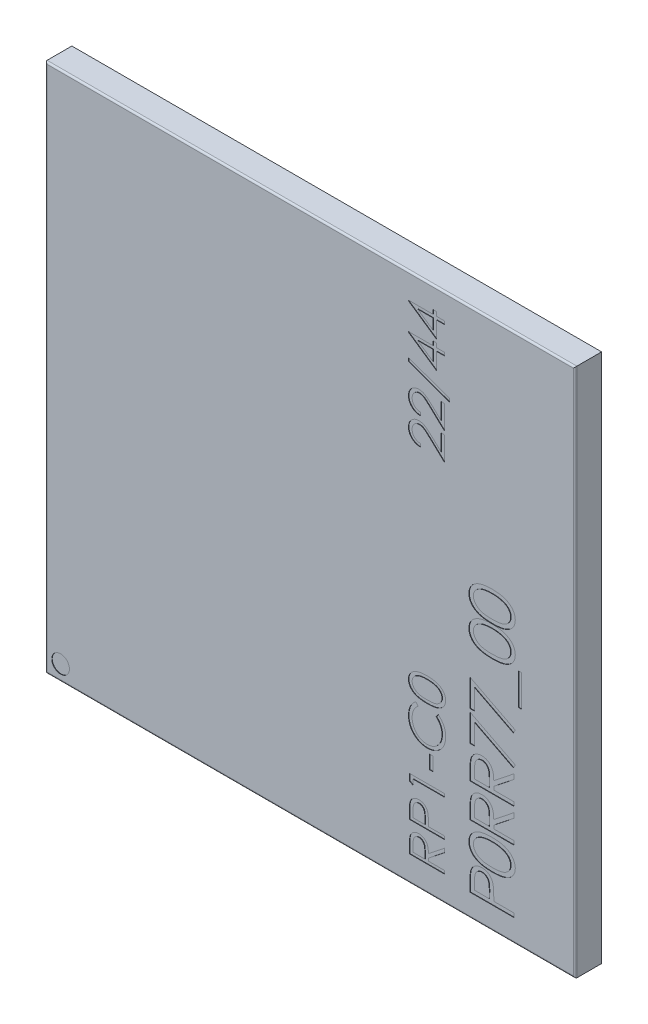
SolidWorks part; units mm, degrees
ref_plane "Płaszczyzna przednia" through (0, 0, 0) normal (0, 0, 1) x (1, 0, 0)
ref_plane "Płaszczyzna górna" through (0, 0, 0) normal (0, 1, 0) x (1, 0, 0)
ref_plane "Płaszczyzna prawa" through (0, 0, 0) normal (1, 0, 0) x (0, 0, -1)
sketch "Sketch1" plane through (0, 0, 0) normal (0, 0, 1) x (1, 0, 0)
  line L1 (6, -6) -> (-6, -6)
  line L2 (6, -6) -> (6, 6)
  line L3 (6, 6) -> (-6, 6)
  line L4 (-6, -6) -> (-6, 6)
  line L5 (6, -6) -> (-6, 6) construction
  line L6 (6, 6) -> (-6, -6) construction
  point P0 (0, 0)
  dimension "D1" = 12
extrude "Boss-Extrude1" add sketch "Sketch1" along normal blind 0.6
fillet "Fillet1" radius 0.04 4 edges at (0, 6, 0.6) (6, 0, 0.6) (0, -6, 0.6) (-6, 0, 0.6)
sketch "Sketch2" plane through (0, 0, 0.6) normal (0, 0, 1) x (1, 0, 0)
  line L0 (1.5285, -1.7789) -> (1.5285, 2.8946) construction
  text T0 "rr"
sketch "Sketch3" plane through (0, 0, 0) normal (0, 0, -1) x (-1, 0, 0)
  line L0 (5.3, -6) -> (5.3, -6.45)
  line L1 (-6, -6) -> (6, -6) construction
  line L2 (5.3, -6.45) -> (5.1, -6.45)
  line L3 (5.1, -6.45) -> (5.1, -6)
  line L4 (5.1, -6) -> (5.3, -6)
  line L5 (6, -6) -> (6, 6) construction
  dimension "D1" = 0.7
  dimension "D2" = 0.2
  dimension "D3" = 0.45
sketch "Sketch5" plane through (0, 0, 0) normal (0, 0, -1) x (-1, 0, 0)
  circle A0 centre (0, 0) radius 2.5
  dimension "D1" = 5
extrude "Boss-Extrude3" add sketch "Sketch5" along normal blind 0.1 separate body
sketch "Szkic1" plane through (0, 0, 0.6) normal (0, 0, 1) x (1, 0, 0)
  line L0 (-49.5686, 13.902) -> (-49.5686, 85.2353) construction
  line L1 (-2.0166, -2.1471) -> (-2.0166, -1.5732)
  line L2 (-2.0166, -1.5732) -> (-1.3854, -1.5732)
  line L3 (-1.3854, -1.5732) -> (-2.0121, -0.9673)
  line L4 (-2.0121, -0.9673) -> (-2.0121, -0.3839)
  line L5 (-2.0121, -0.3839) -> (-1.7715, -0.3839)
  line L6 (-1.7715, -0.3839) -> (-1.7715, -0.5873)
  line L7 (-1.7715, -0.5873) -> (-0.6232, -1.6976)
  line L8 (-0.6232, -1.6976) -> (-0.6232, -2.1471)
  line L9 (-0.6232, -2.1471) -> (-2.0166, -2.1471)
  line L10 (-2.0121, 0) -> (-2.0121, 0.509)
  line L11 (-2.0121, 0.509) -> (-0.9124, -0.1702)
  line L12 (-0.9124, -0.1702) -> (-0.9124, 0.3285)
  line L13 (-0.9124, 0.3285) -> (-0.6232, 0.1498)
  line L14 (-0.6232, 0.1498) -> (-0.6232, -0.8522)
  line L15 (-0.6232, -0.8522) -> (-2.0121, 0)
  line L16 (-2.0121, 1.349) -> (-2.0121, 1.9292)
  line L17 (-2.0121, 1.9292) -> (-0.6232, 1.1584)
  line L18 (-0.6232, 1.1584) -> (-0.6232, 0.5782)
  line L19 (-0.6232, 0.5782) -> (-2.0121, 1.349)
  line L20 (0.3665, -2.3344) -> (0.3665, 2.3764) construction
  line L21 (0.5497, 1.2726) -> (1.1609, 1.2726) construction
  line L22 (1.1526, 1.2019) -> (0.7044, 1.2019)
  line L23 (0.7044, 1.2019) -> (0.7044, 1.0068)
  line L24 (1.1526, 1.3434) -> (0.7044, 1.3434)
  line L25 (0.7044, 1.3434) -> (0.7044, 1.5384)
  line L26 (0.6014, 1.1025) -> (0.6014, 1.4428)
  circle A0 centre (0.8553, 1.2726) radius 0.4116
  arc A1 (0.6014, 1.4428) -> (0.6014, 1.1025) centre (0.8553, 1.2726) ccw
  arc A2 (0.7044, 1.0068) -> (1.1526, 1.2019) centre (0.8553, 1.2726) ccw
  arc A3 (1.1526, 1.3434) -> (0.7044, 1.5384) centre (0.8553, 1.2726) ccw
sketch "Szkic2" plane through (0, 0, 0.6) normal (0, 0, 1) x (1, 0, 0)
  line L0 (3.0467, 5.1197) -> (3.0467, -5.5265) construction
  line L1 (4.6189, -10.8225) -> (4.6189, 5.96) construction
  line L3 (5.96, 5.96) -> (-5.96, 5.96) construction
  line L4 (6, -6) -> (-6, -6) construction
  line L5 (-6, -6) -> (-6, 6) construction
  circle A0 centre (-5.6547, -5.65) radius 0.2
  text T0 "RP1-C0              22/44" font "Century Gothic" height 0.8
  text T1 "P0RR77_00" font "Century Gothic" height 1
  dimension "D1" = 0.4
  dimension "D2" = 0.35
  dimension "D3" = 0.3453
extrude "Wytnij-wyciągnięcie2" cut sketch "Szkic2" against normal blind 0.01
